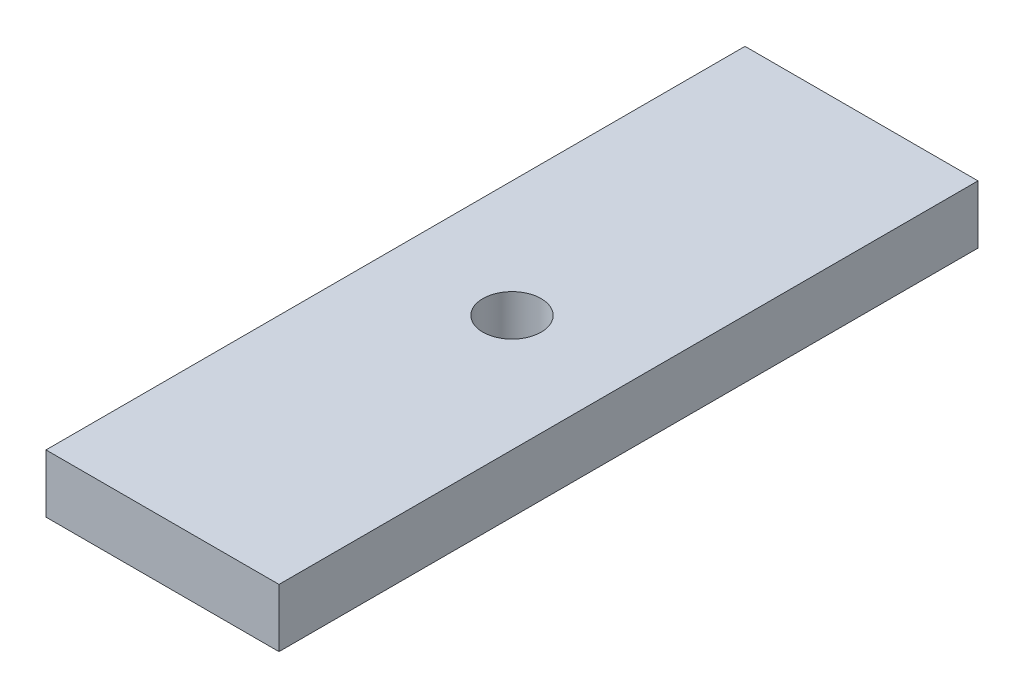
SolidWorks part; units mm, degrees
ref_plane "Front Plane" through (0, 0, 0) normal (0, 0, 1) x (1, 0, 0)
ref_plane "Top Plane" through (0, 0, 0) normal (0, 1, 0) x (1, 0, 0)
ref_plane "Right Plane" through (0, 0, 0) normal (1, 0, 0) x (0, 0, -1)
sketch "Sketch1" plane through (0, 0, 0) normal (0, 1, 0) x (1, 0, 0)
  line L0 (0, 0) -> (40, 0)
  line L1 (40, 0) -> (40, 120)
  line L2 (40, 120) -> (0, 120)
  line L3 (0, 120) -> (0, 0)
  line L4 (0, 60) -> (40, 60)
  circle A0 centre (20, 60) radius 5
extrude "Boss-Extrude1" add sketch "Sketch1" along normal blind 10 contours A0 L4 L1 L2 L3 | A0 L4 L3 L0 L1
